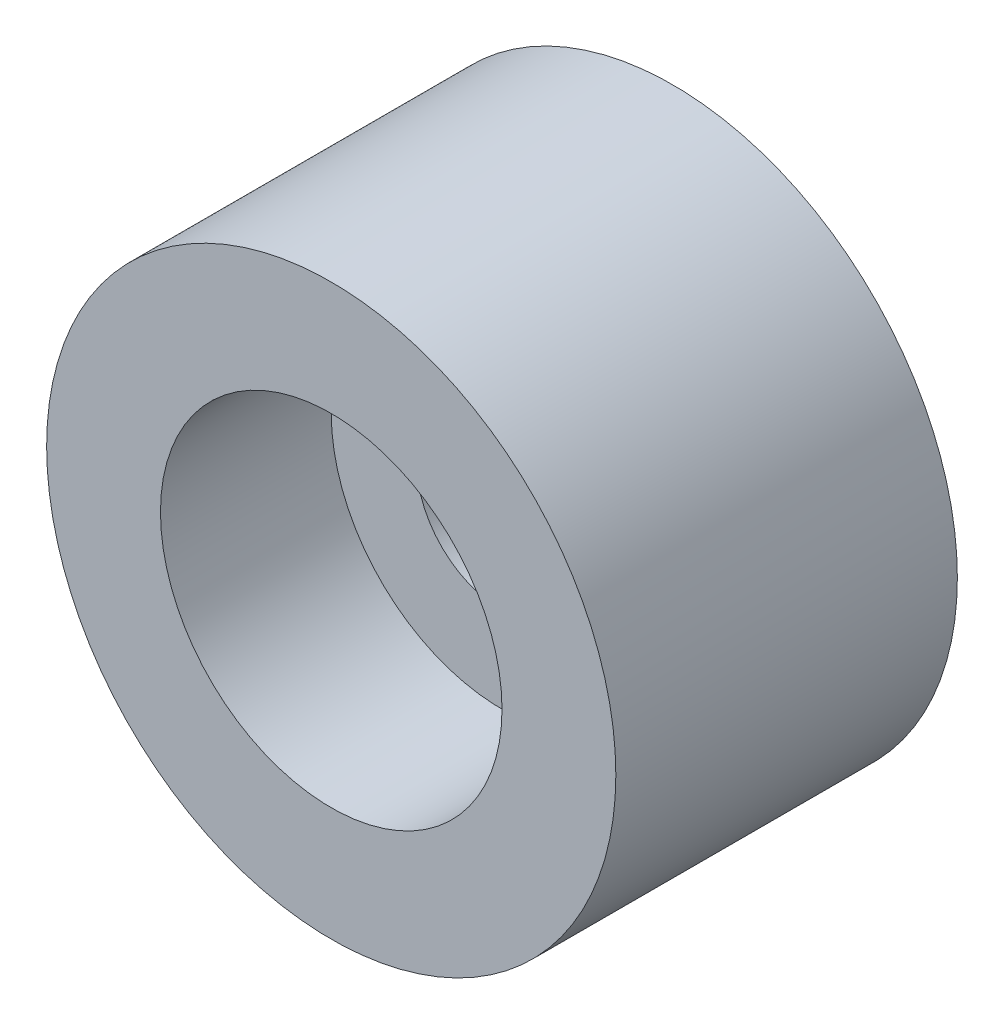
SolidWorks part; units mm, degrees
ref_plane "前视基准面" through (0, 0, 0) normal (0, 0, 1) x (1, 0, 0)
ref_plane "上视基准面" through (0, 0, 0) normal (0, 1, 0) x (1, 0, 0)
ref_plane "右视基准面" through (0, 0, 0) normal (1, 0, 0) x (0, 0, -1)
sketch "草图1" plane through (0, 0, 0) normal (0, 0, 1) x (1, 0, 0)
  circle A0 centre (0, 0) radius 2.5
  circle A1 centre (0, 0) radius 0.75
  dimension "D1" = 5
  dimension "D2" = 1.5
extrude "凸台-拉伸1" add sketch "草图1" along normal blind 3
cosmetic thread "装饰螺纹线1" parameters "D2"=4.5
sketch "草图2" plane through (0, 0, 3) normal (0, 0, 1) x (1, 0, 0)
  circle A0 centre (0, 0) radius 1.5
  dimension "D1" = 3
extrude "切除-拉伸1" cut sketch "草图2" against normal blind 1.5
